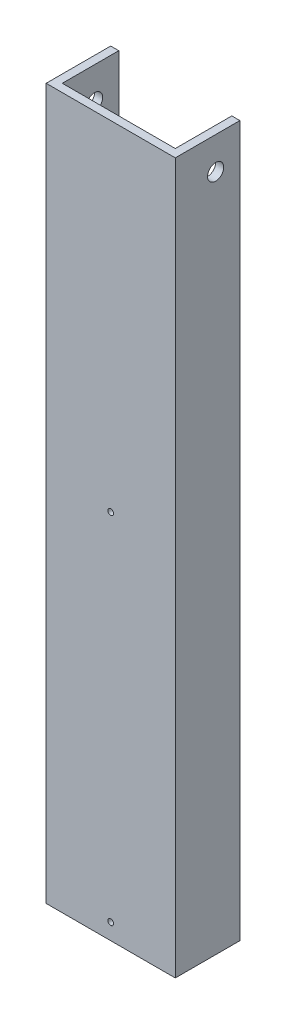
SolidWorks part; units mm, degrees
ref_plane "Front Plane" through (0, 0, 0) normal (0, 0, 1) x (1, 0, 0)
ref_plane "Top Plane" through (0, 0, 0) normal (0, 1, 0) x (1, 0, 0)
ref_plane "Right Plane" through (0, 0, 0) normal (1, 0, 0) x (0, 0, -1)
sketch "Sketch1" plane through (0, 0, 0) normal (0, 1, 0) x (1, 0, 0)
  line L0 (-25.4, 25.4) -> (-25.4, 0)
  line L1 (-25.4, 0) -> (25.4, 0)
  line L2 (25.4, 0) -> (25.4, 25.4)
  line L3 (25.4, 25.4) -> (22.225, 25.4)
  line L4 (22.225, 25.4) -> (22.225, 3.175)
  line L5 (22.225, 3.175) -> (-22.225, 3.175)
  line L6 (-22.225, 3.175) -> (-22.225, 25.4)
  line L7 (-22.225, 25.4) -> (-25.4, 25.4)
  line L8 (0, 0) -> (0, 3.175) construction
  dimension "D1" = 50.8
  dimension "D2" = 25.4
  dimension "D3" = 3.175
extrude "Boss-Extrude1" add sketch "Sketch1" along normal blind 279.4
sketch "Sketch2" plane through (25.4, 0, 0) normal (1, 0, 0) x (0, 0, -1)
  line L0 (0, 279.4) -> (25.4, 279.4) construction
  line L1 (0, 279.4) -> (0, 0) construction
  circle A0 centre (15.875, 266.7) radius 3.175
  dimension "D1" = 6.35
  dimension "D2" = 12.7
  dimension "D3" = 15.875
extrude "Cut-Extrude1" cut sketch "Sketch2" against normal through all
sketch "Sketch3" plane through (0, 0, 0) normal (0, 0, 1) x (1, 0, 0)
  line L2 (0, 146.05) -> (0, 6.35) construction
  line L3 (0, 6.35) -> (0, 0) construction
  dimension "D1" = 139.7
  dimension "D2" = 6.35
hole_wizard "#4-40 Tapped Hole1" positions "Sketch4" profile "Sketch5" tap size "#4-40" standard "ANSI Inch" end condition up to next
sketch "Sketch4" plane through (0, 0, 0) normal (0, 0, 1) x (1, 0, 0)
  point P0 (0, 146.05)
  point P3 (0, 6.35)
sketch "Sketch5" plane through (0, 146.05, 0) normal (1, 0, 0) x (0, -1, 0)
  line L0 (0, 0) -> (0, 3.175)
  line L1 (0, 3.175) -> (1.1303, 3.175)
  line L2 (1.1303, 3.175) -> (1.1303, 0)
  line L5 (1.1303, 0) -> (0, 0)
  line L11 (0, -6.35) -> (0, 107.95) construction
  dimension "Thru Tap Drill Dia." = 2.2606
  dimension "Thru Tap Drill Depth" = 3.175
cosmetic thread "Hole Thread1"
cosmetic thread "Hole Thread2"
equation "\"Thick\"= \"in\""
